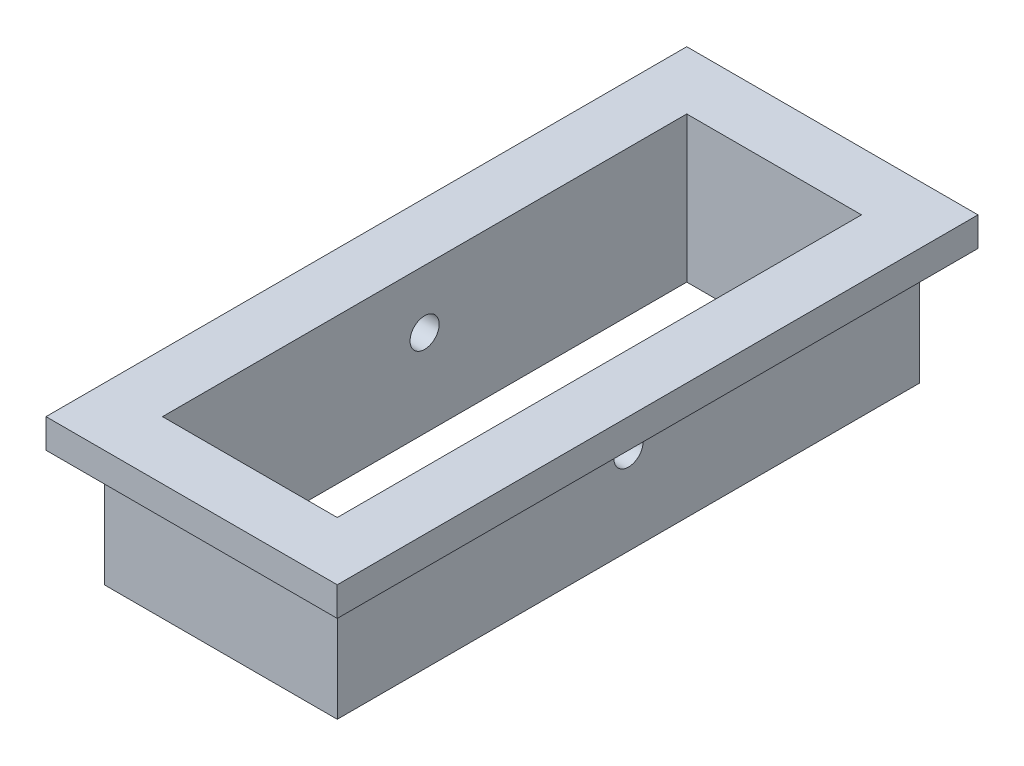
SolidWorks part; units mm, degrees
ref_plane "Front Plane" through (0, 0, 0) normal (0, 0, 1) x (1, 0, 0)
ref_plane "Top Plane" through (0, 0, 0) normal (0, 1, 0) x (1, 0, 0)
ref_plane "Right Plane" through (0, 0, 0) normal (1, 0, 0) x (0, 0, -1)
sketch "Sketch1" plane through (0, 0, 0) normal (0, 1, 0) x (1, 0, 0)
  line L0 (3.81, 11.43) -> (-3.81, 11.43)
  line L1 (5.08, -12.7) -> (-5.08, -12.7)
  line L2 (5.08, -12.7) -> (5.08, 12.7)
  line L3 (5.08, 12.7) -> (-5.08, 12.7)
  line L4 (-5.08, -12.7) -> (-5.08, 12.7)
  line L5 (5.08, -12.7) -> (-5.08, 12.7) construction
  line L6 (5.08, 12.7) -> (-5.08, -12.7) construction
  line L7 (-3.81, -11.43) -> (-3.81, 11.43)
  line L8 (3.81, -11.43) -> (-3.81, -11.43)
  line L9 (3.81, -11.43) -> (3.81, 11.43)
  point P0 (0, 0)
  dimension "D1" = 10.16
  dimension "D2" = 25.4
  dimension "D3" = 1.27
extrude "Boss-Extrude1" add sketch "Sketch1" along normal blind 6.35
sketch "Sketch2" plane through (0, 6.35, 0) normal (0, 1, 0) x (1, 0, 0)
  line L0 (5.08, 12.7) -> (-5.08, 12.7) construction
  line L4 (5.08, -12.7) -> (5.08, 12.7) construction
  line L5 (-5.08, -12.7) -> (5.08, -12.7) construction
  line L6 (-5.08, 12.7) -> (-5.08, -12.7) construction
  line L7 (5.08, 12.7) -> (-5.08, 12.7)
  line L13 (5.08, -12.7) -> (5.08, 12.7)
  line L14 (-5.08, -12.7) -> (5.08, -12.7)
  line L15 (-5.08, 12.7) -> (-5.08, -12.7)
  line L16 (-6.35, 13.97) -> (-6.35, -13.97)
  line L17 (-6.35, -13.97) -> (6.35, -13.97)
  line L18 (6.35, -13.97) -> (6.35, 13.97)
  line L19 (6.35, 13.97) -> (-6.35, 13.97)
  line L20 (-6.35, 13.97) -> (-6.35, -13.97)
  line L21 (-6.35, -13.97) -> (6.35, -13.97)
  line L22 (6.35, -13.97) -> (6.35, 13.97)
  line L23 (6.35, 13.97) -> (-6.35, 13.97)
  dimension "D1" = 1.27
extrude "Boss-Extrude2" add sketch "Sketch2" against normal blind 1.27
sketch "Sketch3" plane through (3.81, 0, 0) normal (-1, 0, 0) x (0, 0, 1)
  line L0 (11.43, 0) -> (-11.43, 0) construction
  circle A0 centre (0, 3.81) radius 0.635
  dimension "D1" = 1.27
  dimension "D2" = 3.81
extrude "Cut-Extrude1" cut sketch "Sketch3" against normal through all both and the other way through all
